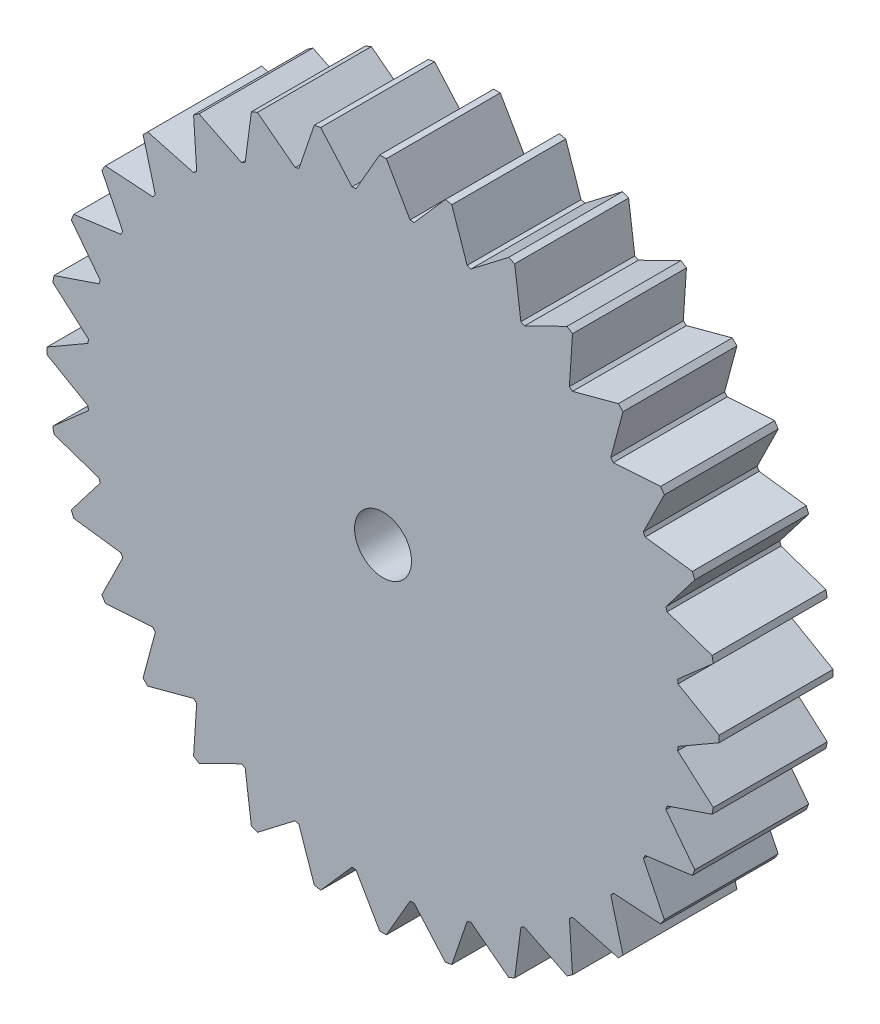
SolidWorks part; units mm, degrees
ref_plane "Front Plane" through (0, 0, 0) normal (0, 0, 1) x (1, 0, 0)
ref_plane "Top Plane" through (0, 0, 0) normal (0, 1, 0) x (1, 0, 0)
ref_plane "Right Plane" through (0, 0, 0) normal (1, 0, 0) x (0, 0, -1)
sketch "Sketch1" plane through (0, 0, 0) normal (0, 0, 1) x (1, 0, 0)
  line L0 (-28.9895, 5.472) -> (-25.8568, 2.7248)
  line L1 (-29.5, -0.2887) -> (-25.8916, -2.372)
  line L2 (-29.5, 0.2887) -> (-25.8916, 2.372)
  line L3 (-28.8768, 6.0383) -> (-28.9895, 5.472)
  line L4 (-29.5, 0) -> (-29.5, 0.2887)
  line L5 (-29.5, 0.2887) -> (-29.5, -0.2887)
  line L6 (-28.8768, 6.0383) -> (-24.9313, 7.3776)
  line L7 (-27.3649, 11.0225) -> (-24.8284, 7.7168)
  line L8 (-27.144, 11.5559) -> (-27.3649, 11.0225)
  line L9 (-27.144, 11.5559) -> (-23.013, 12.0997)
  line L10 (-24.6887, 16.1493) -> (-22.8459, 12.4123)
  line L11 (-24.368, 16.6293) -> (-24.6887, 16.1493)
  line L12 (-24.368, 16.6293) -> (-20.2102, 16.3568)
  line L13 (-21.0638, 20.6555) -> (-19.9854, 16.6308)
  line L14 (-20.6555, 21.0638) -> (-21.0638, 20.6555)
  line L15 (-20.6555, 21.0638) -> (-16.6308, 19.9854)
  line L16 (-16.6293, 24.368) -> (-16.3568, 20.2102)
  line L17 (-16.1493, 24.6887) -> (-16.6293, 24.368)
  line L18 (-16.1493, 24.6887) -> (-12.4123, 22.8459)
  line L19 (-11.5559, 27.144) -> (-12.0997, 23.013)
  line L20 (-11.0225, 27.3649) -> (-11.5559, 27.144)
  line L21 (-11.0225, 27.3649) -> (-7.7168, 24.8284)
  line L22 (-6.0383, 28.8768) -> (-7.3776, 24.9313)
  line L23 (-5.472, 28.9895) -> (-6.0383, 28.8768)
  line L24 (-5.472, 28.9895) -> (-2.7248, 25.8568)
  line L25 (-0.2887, 29.5) -> (-2.372, 25.8916)
  line L26 (0.2887, 29.5) -> (-0.2887, 29.5)
  line L27 (0.2887, 29.5) -> (2.372, 25.8916)
  line L28 (5.472, 28.9895) -> (2.7248, 25.8568)
  line L29 (6.0383, 28.8768) -> (5.472, 28.9895)
  line L30 (6.0383, 28.8768) -> (7.3776, 24.9313)
  line L31 (11.0225, 27.3649) -> (7.7168, 24.8284)
  line L32 (11.5559, 27.144) -> (11.0225, 27.3649)
  line L33 (11.5559, 27.144) -> (12.0997, 23.013)
  line L34 (16.1493, 24.6887) -> (12.4123, 22.8459)
  line L35 (16.6293, 24.368) -> (16.1493, 24.6887)
  line L36 (16.6293, 24.368) -> (16.3568, 20.2102)
  line L37 (20.6555, 21.0638) -> (16.6308, 19.9854)
  line L38 (21.0638, 20.6555) -> (20.6555, 21.0638)
  line L39 (21.0638, 20.6555) -> (19.9854, 16.6308)
  line L40 (24.368, 16.6293) -> (20.2102, 16.3568)
  line L41 (24.6887, 16.1493) -> (24.368, 16.6293)
  line L42 (24.6887, 16.1493) -> (22.8459, 12.4123)
  line L43 (27.144, 11.5559) -> (23.013, 12.0997)
  line L44 (27.3649, 11.0225) -> (27.144, 11.5559)
  line L45 (27.3649, 11.0225) -> (24.8284, 7.7168)
  line L46 (28.8768, 6.0383) -> (24.9313, 7.3776)
  line L47 (28.9895, 5.472) -> (28.8768, 6.0383)
  line L48 (28.9895, 5.472) -> (25.8568, 2.7248)
  line L49 (29.5, 0.2887) -> (25.8916, 2.372)
  line L50 (29.5, -0.2887) -> (29.5, 0.2887)
  line L51 (29.5, -0.2887) -> (25.8916, -2.372)
  line L52 (28.9895, -5.472) -> (25.8568, -2.7248)
  line L53 (28.8768, -6.0383) -> (28.9895, -5.472)
  line L54 (28.8768, -6.0383) -> (24.9313, -7.3776)
  line L55 (27.3649, -11.0225) -> (24.8284, -7.7168)
  line L56 (27.144, -11.5559) -> (27.3649, -11.0225)
  line L57 (27.144, -11.5559) -> (23.013, -12.0997)
  line L58 (24.6887, -16.1493) -> (22.8459, -12.4123)
  line L59 (24.368, -16.6293) -> (24.6887, -16.1493)
  line L60 (24.368, -16.6293) -> (20.2102, -16.3568)
  line L61 (21.0638, -20.6555) -> (19.9854, -16.6308)
  line L62 (20.6555, -21.0638) -> (21.0638, -20.6555)
  line L63 (20.6555, -21.0638) -> (16.6308, -19.9854)
  line L64 (16.6293, -24.368) -> (16.3568, -20.2102)
  line L65 (16.1493, -24.6887) -> (16.6293, -24.368)
  line L66 (16.1493, -24.6887) -> (12.4123, -22.8459)
  line L67 (11.5559, -27.144) -> (12.0997, -23.013)
  line L68 (11.0225, -27.3649) -> (11.5559, -27.144)
  line L69 (11.0225, -27.3649) -> (7.7168, -24.8284)
  line L70 (6.0383, -28.8768) -> (7.3776, -24.9313)
  line L71 (5.472, -28.9895) -> (6.0383, -28.8768)
  line L72 (5.472, -28.9895) -> (2.7248, -25.8568)
  line L73 (0.2887, -29.5) -> (2.372, -25.8916)
  line L74 (-0.2887, -29.5) -> (0.2887, -29.5)
  line L75 (-0.2887, -29.5) -> (-2.372, -25.8916)
  line L76 (-5.472, -28.9895) -> (-2.7248, -25.8568)
  line L77 (-6.0383, -28.8768) -> (-5.472, -28.9895)
  line L78 (-6.0383, -28.8768) -> (-7.3776, -24.9313)
  line L79 (-11.0225, -27.3649) -> (-7.7168, -24.8284)
  line L80 (-11.5559, -27.144) -> (-11.0225, -27.3649)
  line L81 (-11.5559, -27.144) -> (-12.0997, -23.013)
  line L82 (-16.1493, -24.6887) -> (-12.4123, -22.8459)
  line L83 (-16.6293, -24.368) -> (-16.1493, -24.6887)
  line L84 (-16.6293, -24.368) -> (-16.3568, -20.2102)
  line L85 (-20.6555, -21.0638) -> (-16.6308, -19.9854)
  line L86 (-21.0638, -20.6555) -> (-20.6555, -21.0638)
  line L87 (-21.0638, -20.6555) -> (-19.9854, -16.6308)
  line L88 (-24.368, -16.6293) -> (-20.2102, -16.3568)
  line L89 (-24.6887, -16.1493) -> (-24.368, -16.6293)
  line L90 (-24.6887, -16.1493) -> (-22.8459, -12.4123)
  line L91 (-27.144, -11.5559) -> (-23.013, -12.0997)
  line L92 (-27.3649, -11.0225) -> (-27.144, -11.5559)
  line L93 (-27.3649, -11.0225) -> (-24.8284, -7.7168)
  line L94 (-28.8768, -6.0383) -> (-24.9313, -7.3776)
  line L95 (-28.9895, -5.472) -> (-28.8768, -6.0383)
  line L96 (-28.9895, -5.472) -> (-25.8568, -2.7248)
  circle A1 centre (0, 0) radius 2.5
  arc A2 (-24.9313, -7.3776) -> (-24.8284, -7.7168) centre (0, 0) ccw
  arc A3 (-23.013, -12.0997) -> (-22.8459, -12.4123) centre (0, 0) ccw
  arc A4 (-20.2102, -16.3568) -> (-19.9854, -16.6308) centre (0, 0) ccw
  arc A5 (-16.6308, -19.9854) -> (-16.3568, -20.2102) centre (0, 0) ccw
  arc A6 (-12.4123, -22.8459) -> (-12.0997, -23.013) centre (0, 0) ccw
  arc A7 (-7.7168, -24.8284) -> (-7.3776, -24.9313) centre (0, 0) ccw
  arc A8 (-2.7248, -25.8568) -> (-2.372, -25.8916) centre (0, 0) ccw
  arc A9 (2.372, -25.8916) -> (2.7248, -25.8568) centre (0, 0) ccw
  arc A10 (7.3776, -24.9313) -> (7.7168, -24.8284) centre (0, 0) ccw
  arc A11 (12.0997, -23.013) -> (12.4123, -22.8459) centre (0, 0) ccw
  arc A12 (16.3568, -20.2102) -> (16.6308, -19.9854) centre (0, 0) ccw
  arc A13 (19.9854, -16.6308) -> (20.2102, -16.3568) centre (0, 0) ccw
  arc A14 (22.8459, -12.4123) -> (23.013, -12.0997) centre (0, 0) ccw
  arc A15 (24.8284, -7.7168) -> (24.9313, -7.3776) centre (0, 0) ccw
  arc A16 (25.8568, -2.7248) -> (25.8916, -2.372) centre (0, 0) ccw
  arc A17 (25.8916, 2.372) -> (25.8568, 2.7248) centre (0, 0) ccw
  arc A18 (24.9313, 7.3776) -> (24.8284, 7.7168) centre (0, 0) ccw
  arc A19 (23.013, 12.0997) -> (22.8459, 12.4123) centre (0, 0) ccw
  arc A20 (20.2102, 16.3568) -> (19.9854, 16.6308) centre (0, 0) ccw
  arc A21 (16.6308, 19.9854) -> (16.3568, 20.2102) centre (0, 0) ccw
  arc A22 (12.4123, 22.8459) -> (12.0997, 23.013) centre (0, 0) ccw
  arc A23 (7.7168, 24.8284) -> (7.3776, 24.9313) centre (0, 0) ccw
  arc A24 (2.7248, 25.8568) -> (2.372, 25.8916) centre (0, 0) ccw
  arc A25 (-2.372, 25.8916) -> (-2.7248, 25.8568) centre (0, 0) ccw
  arc A26 (-7.3776, 24.9313) -> (-7.7168, 24.8284) centre (0, 0) ccw
  arc A27 (-12.0997, 23.013) -> (-12.4123, 22.8459) centre (0, 0) ccw
  arc A28 (-16.3568, 20.2102) -> (-16.6308, 19.9854) centre (0, 0) ccw
  arc A29 (-19.9854, 16.6308) -> (-20.2102, 16.3568) centre (0, 0) ccw
  arc A30 (-22.8459, 12.4123) -> (-23.013, 12.0997) centre (0, 0) ccw
  arc A31 (-24.8284, 7.7168) -> (-24.9313, 7.3776) centre (0, 0) ccw
  arc A32 (-25.8568, 2.7248) -> (-25.8916, 2.372) centre (0, 0) ccw
  arc A33 (-25.8916, -2.372) -> (-25.8568, -2.7248) centre (0, 0) ccw
  point P137 (0, 0)
  dimension "D2" = 5
  dimension "D3" = 52
  dimension "D4" = 32
extrude "Boss-Extrude1" add sketch "Sketch1" along normal blind 10 contours L1 A33 L96 L95 L94 A2 L93 L92 L91 A3 L90 L89 L88 A4 L87 L86 L85 A5 L84 L83 L82 A6 L81 L80 L79 A7 L78 L77 L76 A8 L75 L74 L73 A9 L72 L71 L70 A10 L69 L68 L67 A11 L66 L65 L64 A12 L63 L62 L61 A13 L60
sketch "Sketch3" plane through (0, 0, 10) normal (0, 0, 1) x (1, 0, 0)
  circle A0 centre (0, 0) radius 2.5
